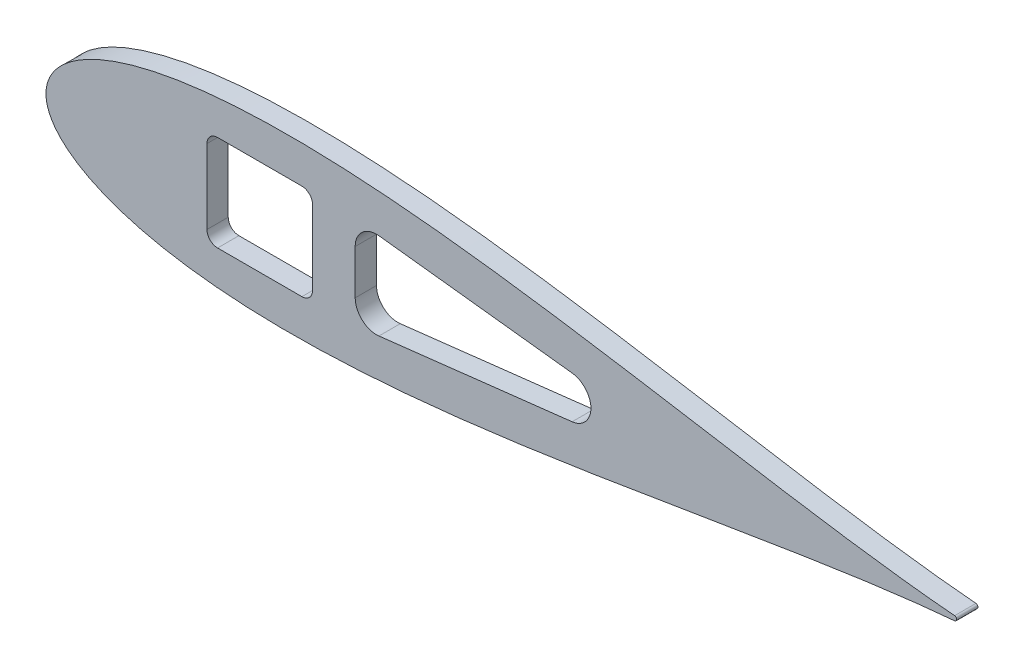
SolidWorks part; units mm, degrees
ref_plane "Front Plane" through (0, 0, 0) normal (0, 0, 1) x (1, 0, 0)
ref_plane "Top Plane" through (0, 0, 0) normal (0, 1, 0) x (1, 0, 0)
ref_plane "Right Plane" through (0, 0, 0) normal (1, 0, 0) x (0, 0, -1)
curve "Curve4"
  spline degree 3 poles (100, 0, 0) (99.8498, 0.0023, 0) (99.4759, 0.008, 0) (99.1023, 0.0238, 0) (98.8789, 0.0332, 0) knots 0 0 0 0 0.401829 1 1 1 1
curve "Curve5"
  spline degree 3 poles (99.3714, -0.0082, 0) (100.2526, 0, 0) (99.3714, 0.0082, 0) (98.8504, 0.035, 0) (97.904, 0.0811, 0) (96.8285, 0.1543, 0) (95.5159, 0.2583, 0) (94.013, 0.3972, 0) (92.313, 0.574, 0) (90.4281, 0.791, 0) (88.3655, 1.0495, 0) (86.1348, 1.3497, 0) (83.7456, 1.691, 0) (81.2082, 2.0715, 0) (78.5335, 2.4886, 0) (75.7326, 2.9386, 0) (72.8172, 3.4168, 0) (69.799, 3.9177, 0) (66.6904, 4.435, 0) (63.5039, 4.9616, 0) (60.2521, 5.4899, 0) (56.948, 6.0119, 0) (53.6049, 6.519, 0) (50.2363, 7.0024, 0) (46.8558, 7.4534, 0) (43.4774, 7.8632, 0) (40.1152, 8.2232, 0) (36.7837, 8.5249, 0) (33.4975, 8.7606, 0) (30.2716, 8.923, 0) (27.1211, 9.0055, 0) (24.0614, 9.0025, 0) (21.108, 8.909, 0) (18.277, 8.7213, 0) (15.5843, 8.4369, 0) (13.0466, 8.0543, 0) (10.6806, 7.5735, 0) (8.5039, 6.996, 0) (6.5349, 6.3253, 0) (4.7933, 5.5673, 0) (3.3001, 4.7321, 0) (2.0777, 3.8366, 0) (1.1467, 2.91, 0) (0.5165, 2.0014, 0) (0.165, 1.1816, 0) (0.0231, 0.524, 0) (-0.0093, 0, 0) (0.0231, -0.524, 0) (0.165, -1.1816, 0) (0.5165, -2.0014, 0) (1.1467, -2.91, 0) (2.0777, -3.8366, 0) (3.3001, -4.7321, 0) (4.7933, -5.5673, 0) (6.5349, -6.3253, 0) (8.5039, -6.996, 0) (10.6806, -7.5735, 0) (13.0466, -8.0543, 0) (15.5843, -8.4369, 0) (18.277, -8.7213, 0) (21.108, -8.909, 0) (24.0614, -9.0025, 0) (27.1211, -9.0055, 0) (30.2716, -8.923, 0) (33.4975, -8.7606, 0) (36.7837, -8.5249, 0) (40.1152, -8.2232, 0) (43.4774, -7.8632, 0) (46.8558, -7.4534, 0) (50.2363, -7.0024, 0) (53.6049, -6.519, 0) (56.948, -6.0119, 0) (60.2521, -5.4899, 0) (63.5039, -4.9616, 0) (66.6904, -4.435, 0) (69.799, -3.9177, 0) (72.8172, -3.4168, 0) (75.7326, -2.9386, 0) (78.5335, -2.4886, 0) (81.2082, -2.0715, 0) (83.7456, -1.691, 0) (86.1348, -1.3497, 0) (88.3655, -1.0495, 0) (90.4281, -0.791, 0) (92.313, -0.574, 0) (94.013, -0.3972, 0) (95.5159, -0.2583, 0) (96.8285, -0.1543, 0) (97.904, -0.0811, 0) (98.8504, -0.035, 0) (99.3714, -0.0082, 0) (100.2526, 0, 0) (99.3714, 0.0082, 0) knots -0.009667 -0.005395 -0.002168 0 0.002168 0.005395 0.009667 0.014967 0.021271 0.028553 0.036781 0.04592 0.055932 0.066773 0.078397 0.090755 0.103793 0.117456 0.131686 0.146422 0.1616 0.177156 0.193024 0.209135 0.225421 0.241812 0.258238 0.274629 0.290914 0.307025 0.322893 0.338448 0.353626 0.368361 0.38259 0.396253 0.40929 0.421647 0.43327 0.444109 0.454119 0.463255 0.471479 0.478755 0.485052 0.490344 0.49461 0.497833 0.5 0.502167 0.50539 0.509656 0.514948 0.521245 0.528521 0.536745 0.545881 0.555891 0.56673 0.578353 0.59071 0.603747 0.61741 0.631639 0.646374 0.661552 0.677107 0.692975 0.709086 0.725371 0.741762 0.758188 0.774579 0.790865 0.806976 0.822844 0.8384 0.853578 0.868314 0.882544 0.896207 0.909245 0.921603 0.933227 0.944068 0.95408 0.963219 0.971447 0.978729 0.985033 0.990333 0.994605 0.997832 1 1.002168 1.005395 1.009667 periodic
sketch "Sketch2" plane through (0, 0, 0) normal (0, 0, 1) x (1, 0, 0)
  line L0 (642.3793, 0) -> (0, 0) construction
  circle A14 centre (642.3793, 0) radius 1.5875 construction
  arc A15 (642.5108, -1.582) -> (642.5108, 1.582) centre (642.3793, 0) ccw
  spline S2 degree 3 poles (666.3448, -0.0547) (672.2538, 0) (666.3448, 0.0547) (662.8509, 0.2344) (656.505, 0.5436) (649.293, 1.0348) (640.4916, 1.7319) (630.4138, 2.6634) (619.0141, 3.8493) (606.375, 5.3044) (592.5439, 7.0376) (577.5855, 9.0506) (561.5643, 11.3389) (544.5497, 13.8907) (526.6141, 16.6877) (507.8326, 19.7051) (488.2827, 22.9117) (468.0444, 26.2704) (447.1994, 29.739) (425.8316, 33.2703) (404.0263, 36.8132) (381.8707, 40.3133) (359.4533, 43.7135) (336.8645, 46.9554) (314.1962, 49.9798) (291.5418, 52.7277) (268.9963, 55.1412) (246.6566, 57.1646) (224.6209, 58.7452) (202.9892, 59.8341) (181.8631, 60.3875) (161.3458, 60.367) (141.542, 59.7399) (122.5581, 58.4818) (104.5023, 56.5743) (87.485, 54.0089) (71.6197, 50.7848) (57.0237, 46.9125) (43.8205, 42.415) (32.1416, 37.3322) (22.1291, 31.7315) (13.9324, 25.7264) (7.6896, 19.5132) (3.4631, 13.4204) (1.1063, 7.9234) (0.1546, 3.5138) (-0.0622, 0) (0.1546, -3.5138) (1.1063, -7.9234) (3.4631, -13.4204) (7.6896, -19.5132) (13.9324, -25.7264) (22.1291, -31.7315) (32.1416, -37.3322) (43.8205, -42.415) (57.0237, -46.9125) (71.6197, -50.7848) (87.485, -54.0089) (104.5023, -56.5743) (122.5581, -58.4818) (141.542, -59.7399) (161.3458, -60.367) (181.8631, -60.3875) (202.9892, -59.8341) (224.6209, -58.7452) (246.6566, -57.1646) (268.9963, -55.1412) (291.5418, -52.7277) (314.1962, -49.9798) (336.8645, -46.9554) (359.4533, -43.7135) (381.8707, -40.3133) (404.0263, -36.8132) (425.8316, -33.2703) (447.1994, -29.739) (468.0444, -26.2704) (488.2827, -22.9117) (507.8326, -19.7051) (526.6141, -16.6877) (544.5497, -13.8907) (561.5643, -11.3389) (577.5855, -9.0506) (592.5439, -7.0376) (606.375, -5.3044) (619.0141, -3.8493) (630.4138, -2.6634) (640.4916, -1.7319) (649.293, -1.0348) (656.505, -0.5436) (662.8509, -0.2344) (666.3448, -0.0547) (672.2538, 0) (666.3448, 0.0547) knots -0.009667 -0.005395 -0.002168 0 0.002168 0.005395 0.009667 0.014967 0.021271 0.028553 0.036781 0.04592 0.055932 0.066773 0.078397 0.090755 0.103793 0.117456 0.131686 0.146422 0.1616 0.177156 0.193024 0.209135 0.225421 0.241812 0.258238 0.274629 0.290914 0.307025 0.322893 0.338448 0.353626 0.368361 0.38259 0.396253 0.40929 0.421647 0.43327 0.444109 0.454119 0.463255 0.471479 0.478755 0.485052 0.490344 0.49461 0.497833 0.5 0.502167 0.50539 0.509656 0.514948 0.521245 0.528521 0.536745 0.545881 0.555891 0.56673 0.578353 0.59071 0.603747 0.61741 0.631639 0.646374 0.661552 0.677107 0.692975 0.709086 0.725371 0.741762 0.758188 0.774579 0.790865 0.806976 0.822844 0.8384 0.853578 0.868314 0.882544 0.896207 0.909245 0.921603 0.933227 0.944068 0.95408 0.963219 0.971447 0.978729 0.985033 0.990333 0.994605 0.997832 1 1.002168 1.005395 1.009667 only from (670.56, 0) to (670.56, 0)
  point P8 (1.2169, -4.6585)
  point P10 (1.2169, 4.6585)
  dimension "D10" = 3.175
extrude "Boss-Extrude1" add sketch "Sketch2" along normal blind 5.4737
extrude "Cut-Extrude4" cut sketch "Sketch7" against normal through all
sketch "Sketch7" plane through (327.9592, -13.7514, 6.35) normal (0, 0, 1) x (1, 0, 0)
  line L1 (-154.9852, -16.7286) -> (-66.0852, -16.7286)
  line L2 (-154.9852, -16.7286) -> (-154.9852, 44.2314)
  line L3 (-154.9852, 44.2314) -> (-66.0852, 44.2314)
  line L4 (-66.0852, -16.7286) -> (-66.0852, 44.2314)
  line L5 (-154.9852, -16.7286) -> (-66.0852, 44.2314) construction
  line L6 (-154.9852, 44.2314) -> (-66.0852, -16.7286) construction
  point P0 (-110.5352, 13.7514)
extrude "Cut-Extrude5" cut sketch "Sketch8" against normal through all
sketch "Sketch8" plane through (327.9592, -13.7514, 6.35) normal (0, 0, 1) x (1, 0, 0)
  circle A0 centre (314.9285, 13.7514) radius 1.2446
scale "Scale1" scale about origin uniform scaling yes scale factor 0.337
sketch "Sketch11" plane through (0, 0, 0) normal (0, 0, -1) x (-1, 0, 0)
  arc A1 (-216.5262, 0.5331) -> (-216.5262, -0.5331) centre (-216.4818, 0) ccw
  arc A2 (-216.5262, 0.5331) -> (-216.5262, -0.5331) centre (-216.4818, 0) ccw
  spline S1 degree 3 poles (2772.1692, -257.6086) (-340.5091, -9.3396) (-270.4443, 4.4628) (-212.4495, -0.8976) (-208.6078, -1.2972) (-204.3484, -1.7876) (-199.6873, -2.3717) (-194.6463, -3.0501) (-189.2472, -3.8212) (-183.5133, -4.6812) (-177.469, -5.6238) (-171.1396, -6.6406) (-164.5513, -7.7212) (-157.731, -8.8531) (-150.7062, -10.022) (-143.5052, -11.2121) (-136.1569, -12.4061) (-128.6904, -13.5856) (-121.1358, -14.7315) (-113.5234, -15.824) (-105.8841, -16.8432) (-98.2496, -17.7692) (-90.6518, -18.5826) (-83.1233, -19.2645) (-75.6972, -19.7971) (-68.4074, -20.1641) (-61.2879, -20.3506) (-54.3735, -20.3437) (-47.6997, -20.1323) (-41.3021, -19.7084) (-35.2173, -19.0655) (-29.4825, -18.201) (-24.1358, -17.1145) (-19.217, -15.8095) (-14.7675, -14.2939) (-10.8317, -12.581) (-7.4575, -10.6935) (-4.6952, -8.6698) (-2.5914, -6.576) (-1.1671, -4.5227) (-0.3728, -2.6702) (-0.0521, -1.1841) (0.0209, 0) (-0.0521, 1.1841) (-0.3728, 2.6702) (-1.1671, 4.5227) (-2.5914, 6.576) (-4.6952, 8.6698) (-7.4575, 10.6935) (-10.8317, 12.581) (-14.7675, 14.2939) (-19.217, 15.8095) (-24.1358, 17.1145) (-29.4825, 18.201) (-35.2173, 19.0655) (-41.3021, 19.7084) (-47.6997, 20.1323) (-54.3735, 20.3437) (-61.2879, 20.3506) (-68.4074, 20.1641) (-75.6972, 19.7971) (-83.1233, 19.2645) (-90.6518, 18.5826) (-98.2496, 17.7692) (-105.8841, 16.8432) (-113.5234, 15.824) (-121.1358, 14.7315) (-128.6904, 13.5856) (-136.1569, 12.4061) (-143.5052, 11.2121) (-150.7062, 10.022) (-157.731, 8.8531) (-164.5513, 7.7212) (-171.1396, 6.6406) (-177.469, 5.6238) (-183.5133, 4.6812) (-189.2472, 3.8212) (-194.6463, 3.0501) (-199.6873, 2.3717) (-204.3484, 1.7876) (-208.6078, 1.2972) (-212.4495, 0.8976) (-270.4441, -4.4628) (-340.5086, 9.3396) (2772.1398, 257.6063) knots -0.335722 -0.335722 -0.335722 -0.335722 0.021271 0.028553 0.036781 0.04592 0.055932 0.066773 0.078397 0.090755 0.103793 0.117456 0.131686 0.146422 0.1616 0.177156 0.193024 0.209135 0.225421 0.241812 0.258238 0.274629 0.290914 0.307025 0.322893 0.338448 0.353626 0.368361 0.38259 0.396253 0.40929 0.421647 0.43327 0.444109 0.454119 0.463255 0.471479 0.478755 0.485052 0.490344 0.49461 0.497833 0.5 0.502167 0.50539 0.509656 0.514948 0.521245 0.528521 0.536745 0.545881 0.555891 0.56673 0.578353 0.59071 0.603747 0.61741 0.631639 0.646374 0.661552 0.677107 0.692975 0.709086 0.725371 0.741762 0.758188 0.774579 0.790865 0.806976 0.822844 0.8384 0.853578 0.868314 0.882544 0.896207 0.909245 0.921603 0.933227 0.944068 0.95408 0.963219 0.971447 0.978729 1.335721 1.335721 1.335721 1.335721 only from (-216.5262, -0.5331) to (-216.5262, 0.5331)
  spline S2 degree 3 poles (-216.5262, -0.5331) (-216.3518, -0.5476) (-215.0376, -0.6583) (-212.4495, -0.8976) (-208.6078, -1.2972) (-204.3484, -1.7876) (-199.6873, -2.3717) (-194.6463, -3.0501) (-189.2472, -3.8212) (-183.5133, -4.6812) (-177.469, -5.6238) (-171.1396, -6.6406) (-164.5513, -7.7212) (-157.731, -8.8531) (-150.7062, -10.022) (-143.5052, -11.2121) (-136.1569, -12.4061) (-128.6904, -13.5856) (-121.1358, -14.7315) (-113.5234, -15.824) (-105.8841, -16.8432) (-98.2496, -17.7692) (-90.6518, -18.5826) (-83.1233, -19.2645) (-75.6972, -19.7971) (-68.4074, -20.1641) (-61.2879, -20.3506) (-54.3735, -20.3437) (-47.6997, -20.1323) (-41.3021, -19.7084) (-35.2173, -19.0655) (-29.4825, -18.201) (-24.1358, -17.1145) (-19.217, -15.8095) (-14.7675, -14.2939) (-10.8317, -12.581) (-7.4575, -10.6935) (-4.6952, -8.6698) (-2.5914, -6.576) (-1.1671, -4.5227) (-0.3728, -2.6702) (-0.0521, -1.1841) (0.0209, 0) (-0.0521, 1.1841) (-0.3728, 2.6702) (-1.1671, 4.5227) (-2.5914, 6.576) (-4.6952, 8.6698) (-7.4575, 10.6935) (-10.8317, 12.581) (-14.7675, 14.2939) (-19.217, 15.8095) (-24.1358, 17.1145) (-29.4825, 18.201) (-35.2173, 19.0655) (-41.3021, 19.7084) (-47.6997, 20.1323) (-54.3735, 20.3437) (-61.2879, 20.3506) (-68.4074, 20.1641) (-75.6972, 19.7971) (-83.1233, 19.2645) (-90.6518, 18.5826) (-98.2496, 17.7692) (-105.8841, 16.8432) (-113.5234, 15.824) (-121.1358, 14.7315) (-128.6904, 13.5856) (-136.1569, 12.4061) (-143.5052, 11.2121) (-150.7062, 10.022) (-157.731, 8.8531) (-164.5513, 7.7212) (-171.1396, 6.6406) (-177.469, 5.6238) (-183.5133, 4.6812) (-189.2472, 3.8212) (-194.6463, 3.0501) (-199.6873, 2.3717) (-204.3484, 1.7876) (-208.6078, 1.2972) (-212.4495, 0.8976) (-215.0376, 0.6583) (-216.3518, 0.5476) (-216.5262, 0.5331) knots 0.020157 0.020157 0.020157 0.020157 0.021271 0.028553 0.036781 0.04592 0.055932 0.066773 0.078397 0.090755 0.103793 0.117456 0.131686 0.146422 0.1616 0.177156 0.193024 0.209135 0.225421 0.241812 0.258238 0.274629 0.290914 0.307025 0.322893 0.338448 0.353626 0.368361 0.38259 0.396253 0.40929 0.421647 0.43327 0.444109 0.454119 0.463255 0.471479 0.478755 0.485052 0.490344 0.49461 0.497833 0.5 0.502167 0.50539 0.509656 0.514948 0.521245 0.528521 0.536745 0.545881 0.555891 0.56673 0.578353 0.59071 0.603747 0.61741 0.631639 0.646374 0.661552 0.677107 0.692975 0.709086 0.725371 0.741762 0.758188 0.774579 0.790865 0.806976 0.822844 0.8384 0.853578 0.868314 0.882544 0.896207 0.909245 0.921603 0.933227 0.944068 0.95408 0.963219 0.971447 0.978729 0.979843 0.979843 0.979843 0.979843
  dimension "D1" = 0
extrude "Boss-Extrude2" add sketch "Sketch11" against normal blind 5.08
sketch "Sketch10" plane through (0, 0, 0) normal (0, 0, 1) x (1, 0, 0)
  line L1 (38.354, -11.4046) -> (63.5212, -11.4046)
  line L2 (38.354, -11.4046) -> (38.354, 11.4046)
  line L3 (38.354, 11.4046) -> (63.5212, 11.4046)
  line L4 (63.5212, -11.4046) -> (63.5212, 11.4046)
  line L5 (38.354, -11.4046) -> (63.5212, 11.4046) construction
  line L6 (38.354, 11.4046) -> (63.5212, -11.4046) construction
  point P0 (50.9376, 0)
  dimension "D1" = 25.1672
  dimension "D2" = 38.354
  dimension "D5" = 22.8092
extrude "Cut-Extrude6" cut sketch "Sketch10" along normal through all
fillet "Fillet1" radius 2.54 4 edges at (63.5212, 11.4046, 2.54) (38.354, 11.4046, 2.54) (38.354, -11.4046, 2.54) (63.5212, -11.4046, 2.54)
sketch "Sketch12" plane through (0, 0, 0) normal (0, 0, -1) x (-1, 0, 0)
  line L0 (-73.6812, -10.998) -> (-73.6812, 10.998)
  line L1 (-73.6812, 10.998) -> (-129.8571, 4.5065)
  line L2 (-129.8571, 4.5065) -> (-129.8571, -4.5065)
  line L3 (-129.8571, -4.5065) -> (-73.6812, -10.998)
  line L4 (-63.5212, -8.8646) -> (-63.5212, 8.8646) construction
  spline S0 degree 3 poles (-216.5262, 0.5331) (-216.3518, 0.5476) (-215.0376, 0.6583) (-212.4495, 0.8976) (-208.6078, 1.2972) (-204.3484, 1.7876) (-199.6873, 2.3717) (-194.6463, 3.0501) (-189.2472, 3.8212) (-183.5133, 4.6812) (-177.469, 5.6238) (-171.1396, 6.6406) (-164.5513, 7.7212) (-157.731, 8.8531) (-150.7062, 10.022) (-143.5052, 11.2121) (-136.1569, 12.4061) (-128.6904, 13.5856) (-121.1358, 14.7315) (-113.5234, 15.824) (-105.8841, 16.8432) (-98.2496, 17.7692) (-90.6518, 18.5826) (-83.1233, 19.2645) (-75.6972, 19.7971) (-68.4074, 20.1641) (-61.2879, 20.3506) (-54.3735, 20.3437) (-47.6997, 20.1323) (-41.3021, 19.7084) (-35.2173, 19.0655) (-29.4825, 18.201) (-24.1358, 17.1145) (-19.217, 15.8095) (-14.7675, 14.2939) (-10.8317, 12.581) (-7.4575, 10.6935) (-4.6952, 8.6698) (-2.5914, 6.576) (-1.1671, 4.5227) (-0.3728, 2.6702) (-0.0521, 1.1841) (0.0209, 0) (-0.0521, -1.1841) (-0.3728, -2.6702) (-1.1671, -4.5227) (-2.5914, -6.576) (-4.6952, -8.6698) (-7.4575, -10.6935) (-10.8317, -12.581) (-14.7675, -14.2939) (-19.217, -15.8095) (-24.1358, -17.1145) (-29.4825, -18.201) (-35.2173, -19.0655) (-41.3021, -19.7084) (-47.6997, -20.1323) (-54.3735, -20.3437) (-61.2879, -20.3506) (-68.4074, -20.1641) (-75.6972, -19.7971) (-83.1233, -19.2645) (-90.6518, -18.5826) (-98.2496, -17.7692) (-105.8841, -16.8432) (-113.5234, -15.824) (-121.1358, -14.7315) (-128.6904, -13.5856) (-136.1569, -12.4061) (-143.5052, -11.2121) (-150.7062, -10.022) (-157.731, -8.8531) (-164.5513, -7.7212) (-171.1396, -6.6406) (-177.469, -5.6238) (-183.5133, -4.6812) (-189.2472, -3.8212) (-194.6463, -3.0501) (-199.6873, -2.3717) (-204.3484, -1.7876) (-208.6078, -1.2972) (-212.4495, -0.8976) (-215.0376, -0.6583) (-216.3518, -0.5476) (-216.5262, -0.5331) knots 0.020157 0.020157 0.020157 0.020157 0.021271 0.028553 0.036781 0.04592 0.055932 0.066773 0.078397 0.090755 0.103793 0.117456 0.131686 0.146422 0.1616 0.177156 0.193024 0.209135 0.225421 0.241812 0.258238 0.274629 0.290914 0.307025 0.322893 0.338448 0.353626 0.368361 0.38259 0.396253 0.40929 0.421647 0.43327 0.444109 0.454119 0.463255 0.471479 0.478755 0.485052 0.490344 0.49461 0.497833 0.5 0.502167 0.50539 0.509656 0.514948 0.521245 0.528521 0.536745 0.545881 0.555891 0.56673 0.578353 0.59071 0.603747 0.61741 0.631639 0.646374 0.661552 0.677107 0.692975 0.709086 0.725371 0.741762 0.758188 0.774579 0.790865 0.806976 0.822844 0.8384 0.853578 0.868314 0.882544 0.896207 0.909245 0.921603 0.933227 0.944068 0.95408 0.963219 0.971447 0.978729 0.979843 0.979843 0.979843 0.979843 construction
  point P3 (-73.6812, 0)
  point P5 (-129.8571, 0)
  point P8 (-63.5212, 0)
  point P9 (-73.6812, -19.888)
  point P10 (-129.8571, -13.3965)
  point P13 (-148.9071, -10.3187)
  point P16 (-148.9071, 10.3188)
  dimension "D1" = 20.6375
  dimension "D2" = 8.89
  dimension "D3" = 8.89
  dimension "D4" = 19.05
  dimension "D5" = 10.16
extrude "Cut-Extrude7" cut sketch "Sketch12" against normal through all
fillet "Fillet2" radius 5.08 2 edges at (73.6812, 10.998, 2.54) (73.6812, -10.998, 2.54)
fillet "Fillet3" radius 5.0572 4 edges at (129.8571, 0, 5.08) (129.8571, -4.5065, 2.54) (129.8571, 4.5065, 2.54) (129.8571, 0, 0)
equation "\"0.5n\"=0"
equation "\"D3@Sketch12\"=\"D2@Sketch12\""
equation "\"D1@Sketch10\"=.898/cos(25deg)"
